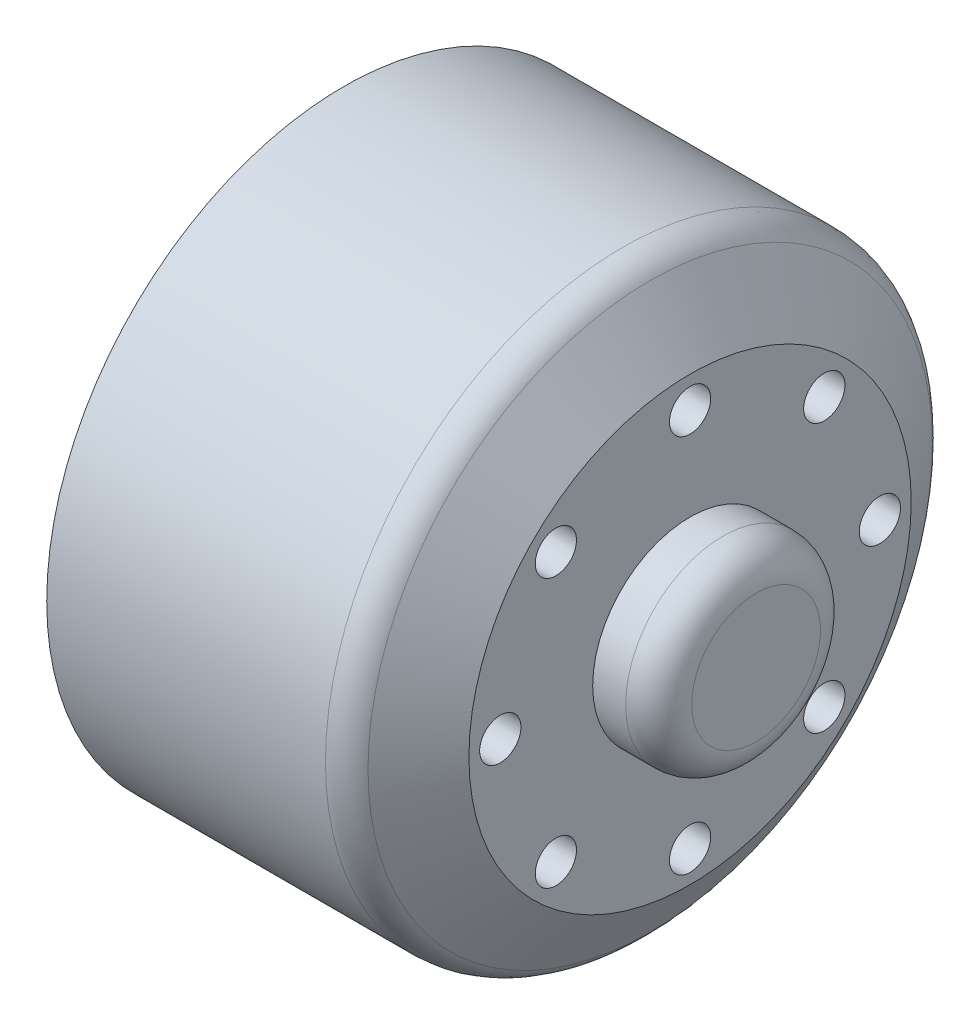
SolidWorks part; units mm, degrees
ref_plane "Front Plane" through (0, 0, 0) normal (0, 0, 1) x (1, 0, 0)
ref_plane "Top Plane" through (0, 0, 0) normal (0, 1, 0) x (1, 0, 0)
ref_plane "Right Plane" through (0, 0, 0) normal (1, 0, 0) x (0, 0, -1)
sketch "Sketch1" plane through (0, 0, 0) normal (0, 1, 0) x (1, 0, 0)
  line L0 (-26.116, 0) -> (40.4037, 0) construction
  line L1 (7.1438, 5.9) -> (7.1438, 13.4)
  line L2 (7.1438, 13.4) -> (4.1337, 18)
  line L3 (4.1337, 18) -> (-13.8362, 18)
  line L4 (-13.8362, 18) -> (-13.8362, 0)
  line L5 (-13.8362, 0) -> (7.1438, 0)
  line L6 (7.1438, 5.9) -> (11.1438, 5.9)
  line L7 (11.1438, 5.9) -> (11.1438, 0)
  line L8 (7.1438, 0) -> (11.1438, 0)
  dimension "D1" = 20.98
  dimension "D2" = 13.4
  dimension "D3" = 123.2
  dimension "D4" = 18
  dimension "D5" = 11.8
  dimension "D6" = 4
revolve "Revolve1" add sketch "Sketch1" angle 360 about L0
sketch "Sketch2" plane through (7.1438, 0, 0) normal (1, 0, 0) x (0, 0, -1)
  circle A0 centre (0, 0) radius 11.5 construction
  circle A1 centre (0, 11.5) radius 1.25
  circle A2 centre (8.1317, 8.1317) radius 1.25
  circle A3 centre (11.5, 0) radius 1.25
  circle A4 centre (8.1317, -8.1317) radius 1.25
  circle A5 centre (0, -11.5) radius 1.25
  circle A6 centre (-8.1317, -8.1317) radius 1.25
  circle A7 centre (-11.5, 0) radius 1.25
  circle A8 centre (-8.1317, 8.1317) radius 1.25
  point P22 (0, 0)
  dimension "D1" = 23
  dimension "D2" = 2.5
  dimension "D3" = 8
extrude "Cut-Extrude1" cut sketch "Sketch2" against normal through all
sketch "Sketch3" plane through (-13.8362, 0, 0) normal (-1, 0, 0) x (0, 0, 1)
  circle A0 centre (0, 0) radius 11.5 construction
  circle A1 centre (0, 11.5) radius 2.5
  circle A2 centre (8.1317, 8.1317) radius 2.5
  circle A3 centre (11.5, 0) radius 2.5
  circle A4 centre (8.1317, -8.1317) radius 2.5
  circle A5 centre (0, -11.5) radius 2.5
  circle A6 centre (-8.1317, -8.1317) radius 2.5
  circle A7 centre (-11.5, 0) radius 2.5
  circle A8 centre (-8.1317, 8.1317) radius 2.5
  point P22 (0, 0)
  dimension "D1" = 23
  dimension "D2" = 5
  dimension "D3" = 8
extrude "Cut-Extrude2" cut sketch "Sketch3" against normal offset from surface (15.98 mm away) 5 up to face at (7.1438, 11.5, -1.25)
sketch "Sketch4" plane through (-13.8362, 0, 0) normal (-1, 0, 0) x (0, 0, 1)
  circle A0 centre (0, 0) radius 9.5
  dimension "D1" = 19
extrude "Cut-Extrude3" cut sketch "Sketch4" against normal blind 10
fillet "Fillet1" radius 2 1 edges at (11.1438, 0, 5.9)
fillet "Fillet2" radius 2 1 edges at (4.1337, 0, 18)
